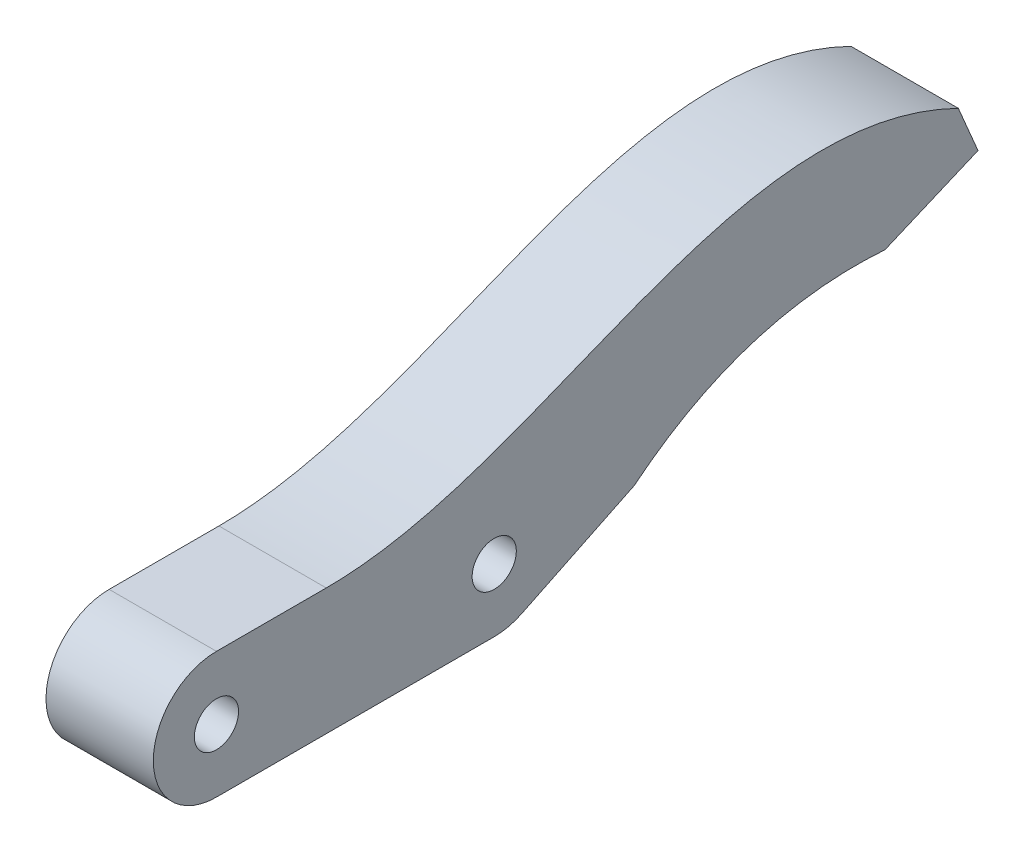
SolidWorks part; units mm, degrees
ref_plane "Front Plane" through (0, 0, 0) normal (0, 0, 1) x (1, 0, 0)
ref_plane "Top Plane" through (0, 0, 0) normal (0, 1, 0) x (1, 0, 0)
ref_plane "Right Plane" through (0, 0, 0) normal (1, 0, 0) x (0, 0, -1)
sketch "Sketch1" plane through (0, 0, 0) normal (1, 0, 0) x (0, 0, -1)
  line L1 (0, 0) -> (27, 0)
  line L2 (0, 0) -> (0, 10)
  line L3 (0, 10) -> (27, 10)
  circle A0 centre (5, 5) radius 1.75
  circle A1 centre (5, 5) radius 5
  circle A2 centre (27, 5) radius 5
  circle A3 centre (27, 5) radius 1.75
  dimension "D7" = 3.5
  dimension "D11" = 10
  dimension "D2" = 3.5
  dimension "D1" = 10
  dimension "D8" = 5
  dimension "D9" = 5
  dimension "D10" = 22
extrude "Boss-Extrude1" add sketch "Sketch1" along normal blind 8.5 contours A1 A0 | A2 L3 A1 L1 | A2 A3 | L2 A1 | L1 A1
sketch "Sketch2" plane through (8.5, 0, 0) normal (1, 0, 0) x (0, 0, -1)
  line L6 (5, 10) -> (27, 10) construction
  line L14 (5, 10) -> (27, 10)
  line L20 (29.1838, 0.5021) -> (38.0854, 4.8241)
  line L21 (57.948, 11.0678) -> (65.3138, 14.1895)
  line L22 (65.3138, 14.1895) -> (63.753, 17.8724)
  arc A3 (27, 0) -> (27, 10) centre (27, 5) ccw construction
  arc A4 (27, 0) -> (27, 10) centre (27, 5) ccw
  spline S0 degree 2 poles (38.0854, 4.8241) (46.7975, 11.8952) (57.948, 11.0678) knots 0 0 0 1 1 1
  spline S1 degree 3 poles (63.753, 17.8724) (45.9289, 26.5638) (31.0593, 10) (13.695, 10) knots 0 0 0 0 1 1 1 1
  point P2 (27, 5)
  dimension "D3" = 4
  dimension "D4" = 8
extrude "Boss-Extrude2" add sketch "Sketch2" against normal blind 8.5
